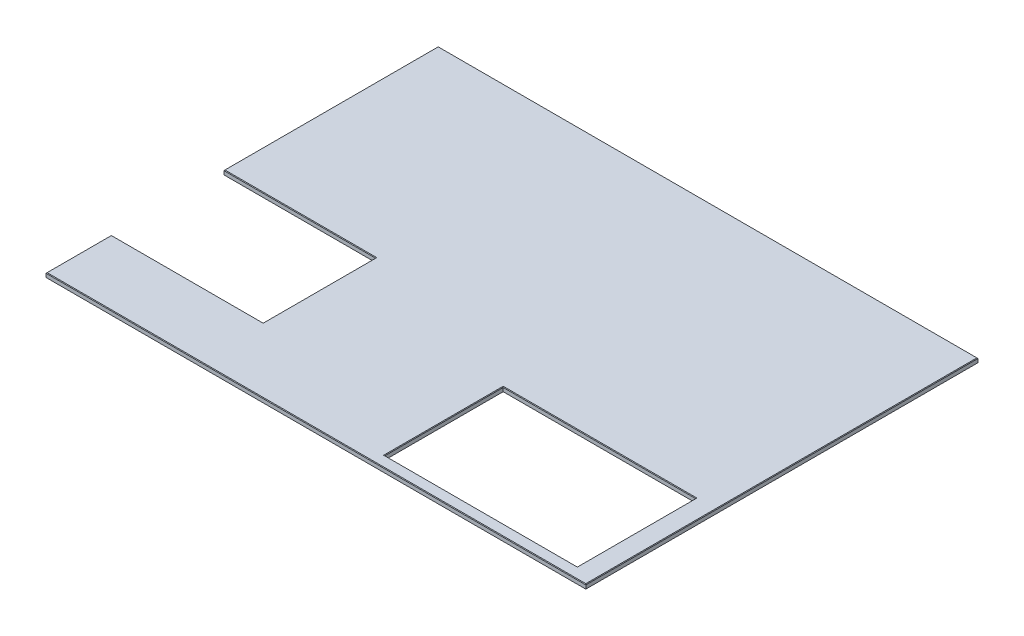
SolidWorks part; units mm, degrees
material "Oak"
ref_plane "Front Plane" through (0, 0, 0) normal (0, 0, 1) x (1, 0, 0)
ref_plane "Top Plane" through (0, 0, 0) normal (0, 1, 0) x (1, 0, 0)
ref_plane "Right Plane" through (0, 0, 0) normal (1, 0, 0) x (0, 0, -1)
sketch "Sketch1" plane through (0, 0, 0) normal (0, 1, 0) x (1, 0, 0)
  line L0 (1479.4865, 50.8) -> (1479.4865, 585.724)
  line L1 (1479.4865, 585.724) -> (2349.4365, 585.724)
  line L2 (2349.4365, 585.724) -> (2349.4365, 50.8)
  line L4 (2438.4, 0) -> (2438.4, 1771.65)
  line L5 (2438.4, 1771.65) -> (0, 1771.65)
  line L6 (0, 1771.65) -> (0, 803.275)
  line L7 (0, 0) -> (2438.4, 0)
  line L8 (0, 295.275) -> (0, 0)
  line L9 (0, 803.275) -> (685.8, 803.275)
  line L11 (0, 295.275) -> (685.8, 295.275)
  line L12 (685.8, 803.275) -> (685.8, 295.275)
  line L14 (1479.4865, 50.8) -> (2349.4365, 50.8)
  dimension "D1" = 2438.4
  dimension "D2" = 1479.4865
  dimension "D3" = 869.95
  dimension "D4" = 534.924
  dimension "D5" = 1771.65
  dimension "D6" = 685.8
  dimension "D7" = 295.275
  dimension "D8" = 508
  dimension "D9" = 50.8
extrude "Boss-Extrude1" add sketch "Sketch1" against normal blind 19.05
chamfer "Chamfer1" distance 2.54 angle 45 12 edges at (0, 0, -1287.4625) (1219.2, 0, -1771.65) (2438.4, 0, -885.825) (2349.4365, 0, -318.262) (1914.4615, 0, -585.724) (1479.4865, 0, -318.262) (1219.2, 0, 0) (0, 0, -147.6375) (342.9, 0, -295.275) (685.8, 0, -549.275) (342.9, 0, -803.275) (1914.4615, 0, -50.8)
